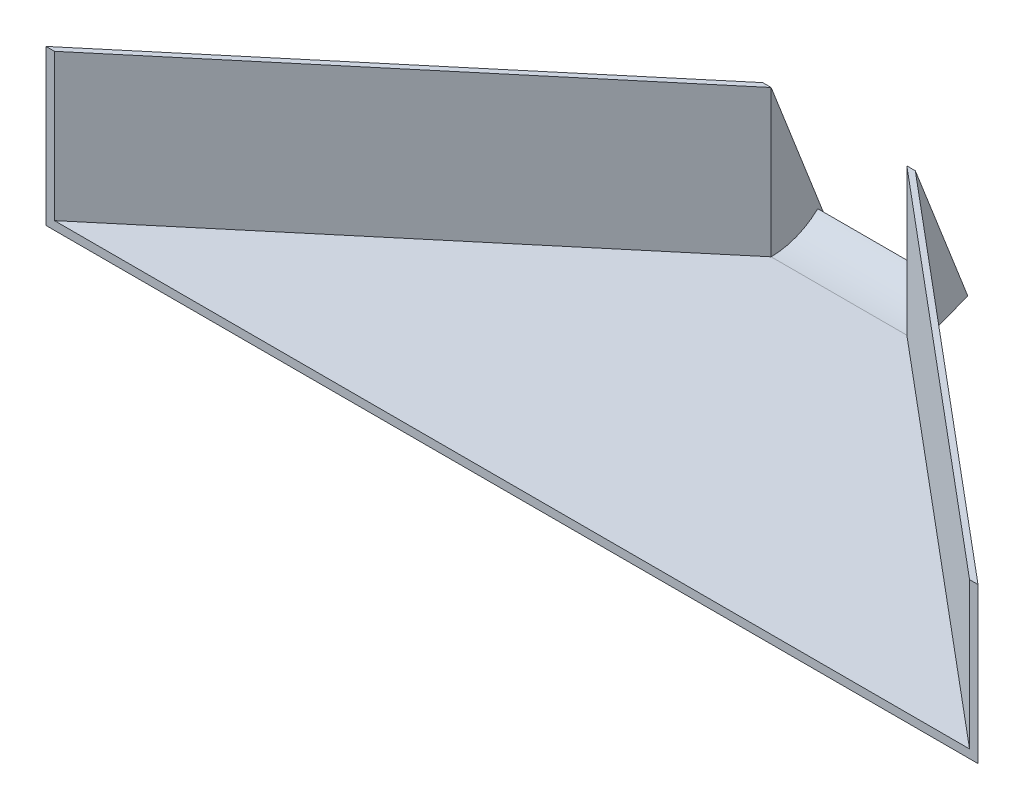
SolidWorks part; units mm, degrees
ref_plane "Front Plane" through (0, 0, 0) normal (0, 0, 1) x (1, 0, 0)
ref_plane "Top Plane" through (0, 0, 0) normal (0, 1, 0) x (1, 0, 0)
ref_plane "Right Plane" through (0, 0, 0) normal (1, 0, 0) x (0, 0, -1)
sketch "Sketch1" plane through (0, 0, 0) normal (0, 1, 0) x (1, 0, 0)
  line L0 (0, 0) -> (44.45, 0)
  line L1 (0, 0) -> (-127.635, -107.0985)
  line L2 (44.45, 0) -> (172.085, -107.0985)
  line L3 (-127.635, -107.0985) -> (172.085, -107.0985)
  dimension "D1" = 44.45
  dimension "D2" = 40
  dimension "D3" = 40
  dimension "D4" = 299.72
extrude "Boss-Extrude1" add sketch "Sketch1" along normal blind 2.7686
sketch "Sketch2" plane through (0, 2.7686, 0) normal (0, 1, 0) x (1, 0, 0)
  line L0 (0, 0) -> (-127.635, -107.0985)
  line L2 (-130.4036, -107.0985) -> (-2.7686, 0)
  line L3 (-2.7686, 0) -> (0, 0)
  line L4 (-130.4036, -107.0985) -> (-127.635, -107.0985)
  line L5 (44.45, 0) -> (47.2186, 0)
  line L6 (47.2186, 0) -> (174.8536, -107.0985)
  line L7 (174.8536, -107.0985) -> (172.085, -107.0985)
  line L8 (44.45, 0) -> (172.085, -107.0985)
  dimension "D1" = 2.7686
  dimension "D2" = 2.7686
  dimension "D3" = 2.7686
  dimension "D4" = 2.7686
extrude "Boss-Extrude2" add sketch "Sketch2" along normal blind 50.8 from surface at -2.7686 separate body starting at face at (22.225, 0, 53.5492)
ref_plane "Plane1" through (44.45, 0, 0) normal (1, 0, 0) x (0, 0, -1)
sketch "Sketch4" plane through (0, 0, 0) normal (0, 0, -1) x (-1, 0, 0)
  line L0 (-47.2186, 50.8) -> (-44.45, 50.8)
  line L1 (-44.45, 50.8) -> (-44.45, 0)
  line L2 (-44.45, 0) -> (-47.2186, 0)
  line L3 (-47.2186, 0) -> (-44.45, 0) construction
  line L4 (-47.2186, 50.8) -> (-47.2186, 0) construction
  line L5 (-47.2186, 0) -> (-47.2186, 50.8)
extrude "Boss-Extrude3" add sketch "Sketch4" along normal blind 25.4
sketch "Sketch5" plane through (47.2186, 0, 0) normal (1, 0, 0) x (0, 0, -1)
  line L0 (17.186, 6.6971) -> (0, 0)
  line L1 (0, 0) -> (25.4, 0)
  line L2 (25.4, 0) -> (25.4, 14.2449)
  line L3 (17.186, 6.6971) -> (176.1609, 152.7785) construction
  line L4 (25.4, 50.8) -> (25.4, 0) construction
  line L5 (25.4, 14.2449) -> (25.4, 50.8)
  line L6 (25.4, 50.8) -> (0, 50.8)
  line L7 (0, 50.8) -> (17.186, 6.6971)
extrude "Cut-Extrude1" cut sketch "Sketch5" against normal up to surface (47.2186 mm away)
sketch "Sketch10" plane through (44.45, 0, 0) normal (-1, 0, 0) x (0, 0, 1)
  line L0 (-17.186, 6.6971) -> (-15.2981, 8.7516)
  line L2 (-17.186, 6.6971) -> (0, 0)
  line L3 (0, 0) -> (0, 2.7686)
  arc A0 (0, 2.7686) -> (-15.2981, 8.7516) centre (0, 25.3182) cw
extrude "Boss-Extrude6" add sketch "Sketch10" along normal up to surface (44.45 mm away)
ref_plane "Plane2" through (22.225, 0, 0) normal (-1, 0, 0) x (0, 0, 1)
mirror "Mirror1" about plane through (22.225, 0, 0) normal (-1, 0, 0) of "Boss-Extrude3"
mirror "Mirror2" about plane through (22.225, 0, 0) normal (-1, 0, 0) of "Cut-Extrude1"
